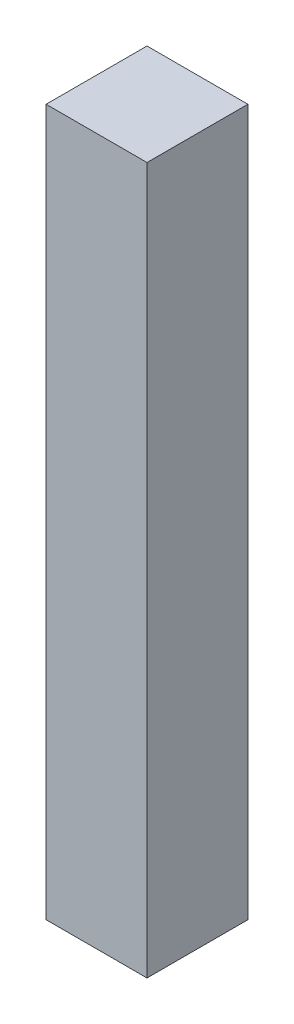
SolidWorks part; units mm, degrees
ref_plane "Plan de face" through (0, 0, 0) normal (0, 0, 1) x (1, 0, 0)
ref_plane "Plan de dessus" through (0, 0, 0) normal (0, 1, 0) x (1, 0, 0)
ref_plane "Plan de droite" through (0, 0, 0) normal (1, 0, 0) x (0, 0, -1)
sketch "Esquisse1" plane through (0, 0, 0) normal (0, 1, 0) x (1, 0, 0)
  line L1 (-25, -25) -> (25, -25)
  line L2 (-25, -25) -> (-25, 25)
  line L3 (-25, 25) -> (25, 25)
  line L4 (25, -25) -> (25, 25)
  line L5 (-25, -25) -> (25, 25) construction
  line L6 (-25, 25) -> (25, -25) construction
  point P0 (0, 0)
  dimension "D1" = 50
extrude "Boss.-Extru.1" add sketch "Esquisse1" along normal blind 350
